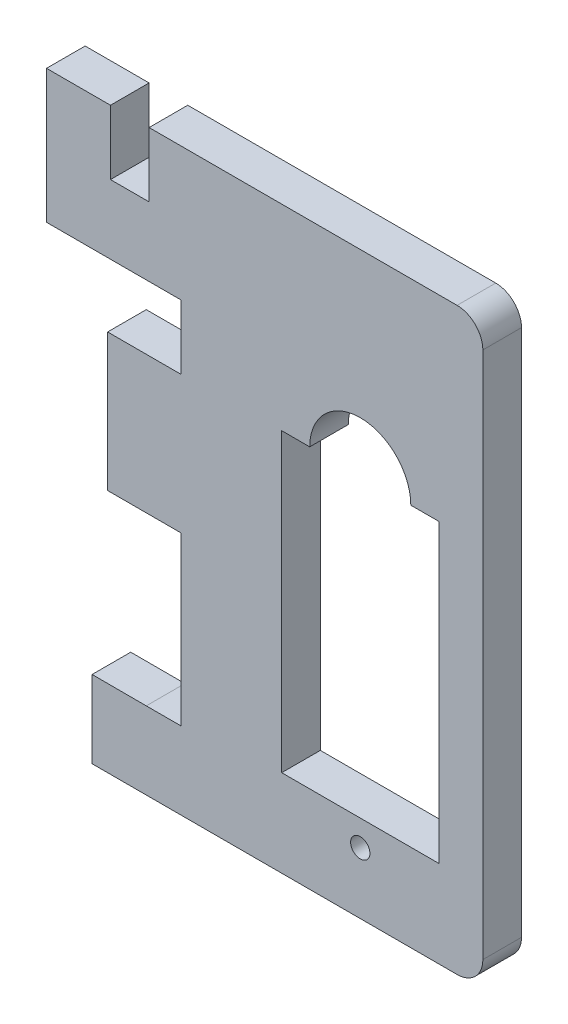
SolidWorks part; units mm, degrees
material "Acrylic (Medium-high impact)"
ref_plane "Front Plane" through (0, 0, 0) normal (0, 0, 1) x (1, 0, 0)
ref_plane "Top Plane" through (0, 0, 0) normal (0, 1, 0) x (1, 0, 0)
ref_plane "Right Plane" through (0, 0, 0) normal (1, 0, 0) x (0, 0, -1)
sketch "Sketch1" plane through (0, 0, 0) normal (0, 0, 1) x (1, 0, 0)
  line L0 (-29.7618, -16.735) -> (-29.7618, -27.4013)
  line L1 (-34.5064, -1.3778) -> (-29.5401, -1.3778)
  line L3 (-27.7618, -46.3778) -> (-2.6245, -46.3778)
  line L4 (-0.6245, -3.3778) -> (-0.6245, -44.3778)
  line L14 (-26.5401, -1.3778) -> (-2.6245, -1.3778)
  line L16 (-29.5401, -1.3778) -> (-29.5401, -6.3778)
  line L17 (-29.5401, -6.3778) -> (-26.5401, -6.3778)
  line L18 (-26.5401, -1.3778) -> (-26.5401, -6.3778)
  line L23 (-29.7618, -11.735) -> (-24.065, -11.735)
  line L24 (-24.065, -11.735) -> (-24.065, -16.735)
  line L25 (-24.065, -16.735) -> (-29.7618, -16.735)
  line L26 (-29.7618, -27.4013) -> (-24.065, -27.4013)
  line L27 (-24.065, -27.4013) -> (-24.065, -40.3801)
  line L28 (-24.065, -40.3801) -> (-26.7618, -40.3801)
  line L29 (-26.7618, -40.3801) -> (-30.9666, -40.3722)
  line L33 (-30.9666, -40.3722) -> (-30.9666, -46.3778)
  line L35 (-30.9666, -46.3778) -> (-27.7618, -46.3778)
  line L36 (-34.5064, -1.3778) -> (-34.5064, -11.735)
  line L37 (-24.0618, -11.735) -> (-36.0618, -11.735) construction
  line L38 (-34.5064, -11.735) -> (-29.7618, -11.735)
  arc A1 (-2.6245, -46.3778) -> (-0.6245, -44.3778) centre (-2.6245, -44.3778) ccw
  arc A2 (-2.6245, -1.3778) -> (-0.6245, -3.3778) centre (-2.6245, -3.3778) cw
  point P18 (-27.6266, -46.3271)
  point P21 (-0.6245, -46.3778)
  point P26 (-29.7618, -1.3778)
  dimension "D2" = 45
  dimension "D5" = 5
  dimension "D6" = 3
extrude "Boss-Extrude1" add sketch "Sketch1" along normal blind 3
sketch "Sketch2" plane through (0, 0, 3) normal (0, 0, 1) x (1, 0, 0)
  line L1 (-16.2431, -16.6158) -> (-4.0431, -16.6158)
  line L2 (-16.2431, -16.6158) -> (-16.2431, -39.6158)
  line L3 (-16.2431, -39.6158) -> (-4.0431, -39.6158)
  line L4 (-4.0431, -16.6158) -> (-4.0431, -39.6158)
  dimension "D1" = 23
  dimension "D2" = 12.2
extrude "Cut-Extrude1" cut sketch "Sketch2" against normal through all
sketch "Sketch5" plane through (0, 0, 3) normal (0, 0, 1) x (1, 0, 0)
  line L0 (-4.0431, -16.6158) -> (-16.2431, -16.6158) construction
  line L1 (-10.1431, -39.6158) -> (-10.1431, -41.6158) construction
  line L2 (-16.2431, -39.6158) -> (-4.0431, -39.6158) construction
  circle A0 centre (-10.1431, -16.6158) radius 3.925
  circle A1 centre (-10.1431, -41.6158) radius 0.75
  dimension "D1" = 7.85
  dimension "D3" = 1.5
  dimension "D2" = 2
extrude "Cut-Extrude2" cut sketch "Sketch5" against normal blind 3
